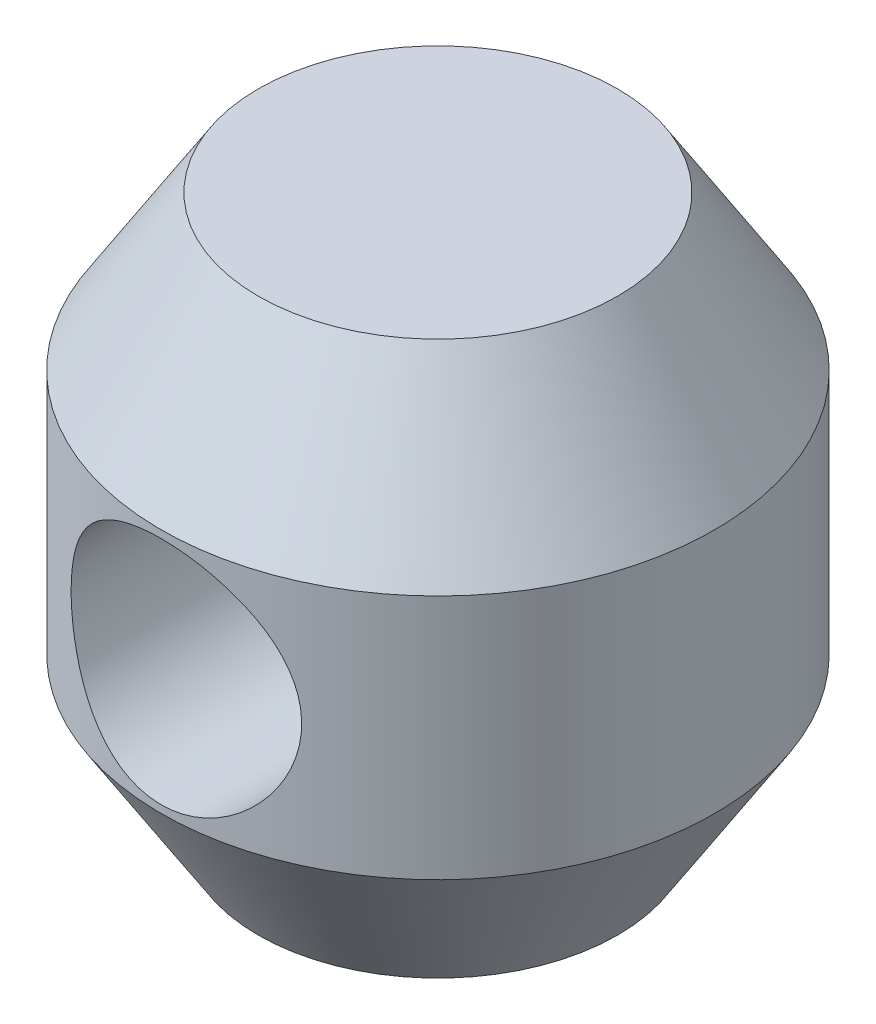
SolidWorks part; units mm, degrees
ref_plane "Front Plane" through (0, 0, 0) normal (0, 0, 1) x (1, 0, 0)
ref_plane "Top Plane" through (0, 0, 0) normal (0, 1, 0) x (1, 0, 0)
ref_plane "Right Plane" through (0, 0, 0) normal (1, 0, 0) x (0, 0, -1)
sketch "Sketch1" plane through (0, 0, 0) normal (0, 0, 1) x (1, 0, 0)
  line L0 (0, 20.8294) -> (0, 9.525) construction
  line L1 (0, 9.525) -> (0, -9.525)
  line L2 (6.1843, -9.525) -> (9.525, -4.2296)
  line L3 (9.525, -4.2296) -> (9.525, 4.2296)
  line L4 (9.525, 4.2296) -> (6.1843, 9.525)
  line L5 (0, 0) -> (9.525, 0) construction
  line L6 (0, 9.525) -> (0, -9.525) construction
  line L7 (6.1843, 9.525) -> (0, 9.525)
  line L8 (6.1843, -9.525) -> (0, -9.525)
  line L9 (0, -9.525) -> (0, -17.3579) construction
  arc A0 (0, -9.525) -> (0, 9.525) centre (0, 0) ccw construction
  dimension "D1" = 19.05
revolve "Revolve1" add sketch "Sketch1" angle 360 about L0
sketch "Sketch3" plane through (0, 9.525, 0) normal (0, 0, -1) x (0, 1, 0)
  circle A0 centre (-9.525, 0) radius 3.9688
  dimension "D1" = 7.9375
extrude "Cut-Extrude1" cut sketch "Sketch3" against normal through all and the other way through all
